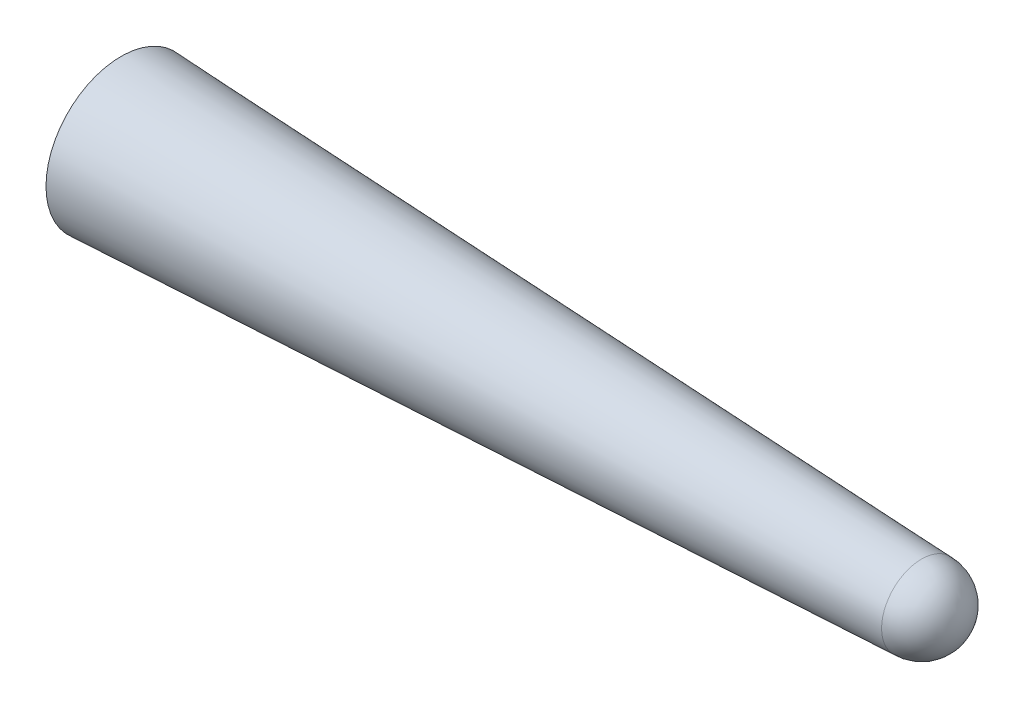
SolidWorks part; units mm, degrees
ref_plane "Front Plane" through (0, 0, 0) normal (0, 0, 1) x (1, 0, 0)
ref_plane "Top Plane" through (0, 0, 0) normal (0, 1, 0) x (1, 0, 0)
ref_plane "Right Plane" through (0, 0, 0) normal (1, 0, 0) x (0, 0, -1)
sketch "Sketch1" plane through (0, 0, 0) normal (0, 0, 1) x (1, 0, 0)
  line L0 (-105.6096, -24.1918) -> (-21.6096, -24.1918) construction
  line L1 (-105.6096, -24.1918) -> (-105.6096, -16.6918)
  line L2 (-105.6096, -16.6918) -> (-25.6096, -20.1918)
  line L3 (-105.6096, -24.1918) -> (-21.6096, -24.1918)
  arc A0 (-25.6096, -20.1918) -> (-21.6096, -24.1918) centre (-25.6096, -24.1918) cw
  dimension "D2" = 7.5
revolve "Revolve1" add sketch "Sketch1" angle 360 about L0
